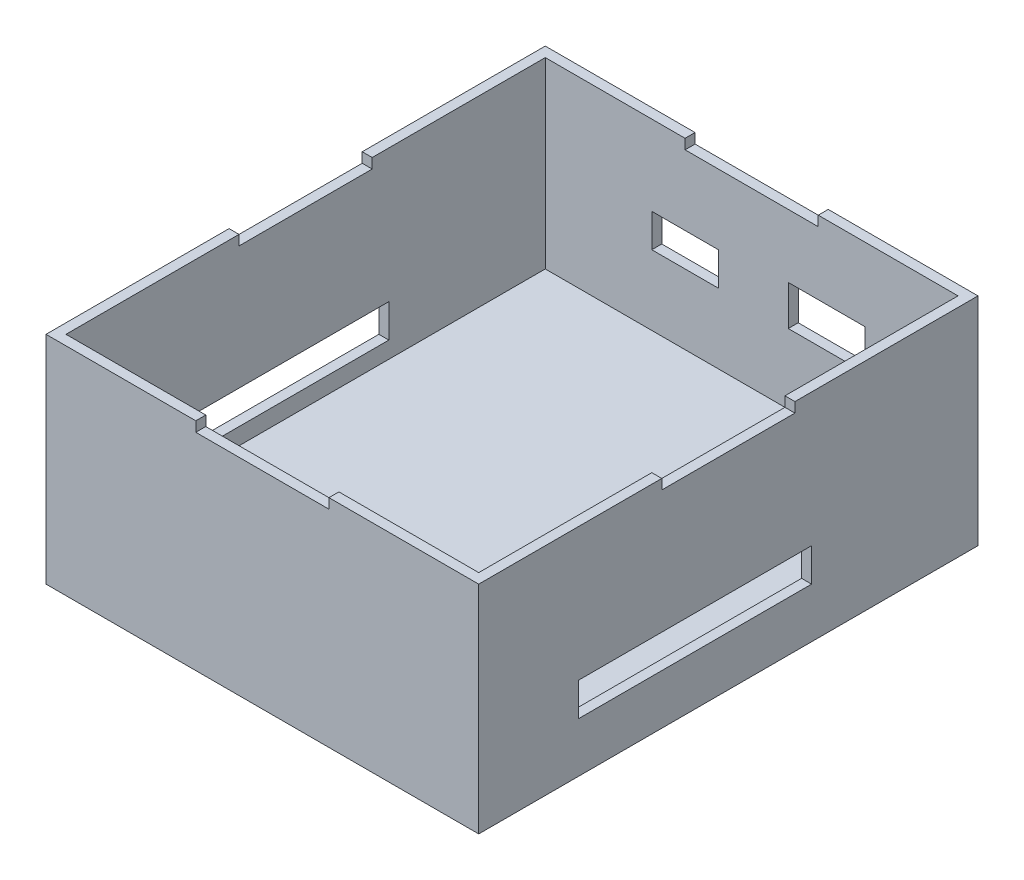
SolidWorks part; units mm, degrees
ref_plane "Plano frontal" through (0, 0, 0) normal (0, 0, 1) x (1, 0, 0)
ref_plane "Plano superior" through (0, 0, 0) normal (0, 1, 0) x (1, 0, 0)
ref_plane "Plano direito" through (0, 0, 0) normal (1, 0, 0) x (0, 0, -1)
sketch "Esboço1" plane through (0, 0, 0) normal (0, 0, 1) x (1, 0, 0)
  line L1 (-52.9398, 41.4834) -> (77.0602, 41.4834)
  line L2 (-52.9398, 41.4834) -> (-52.9398, -23.5166)
  line L3 (-52.9398, -23.5166) -> (77.0602, -23.5166)
  line L4 (77.0602, 41.4834) -> (77.0602, -23.5166)
  dimension "D1" = 130
  dimension "D2" = 65
extrude "Ressalto-extrusão1" add sketch "Esboço1" along normal blind 150
sketch "Esboço2" plane through (-52.9398, 0, 0) normal (-1, 0, 0) x (0, 0, 1)
  line L1 (50, 1.4834) -> (120, 1.4834)
  line L2 (50, 1.4834) -> (50, -8.5166)
  line L3 (50, -8.5166) -> (120, -8.5166)
  line L4 (120, 1.4834) -> (120, -8.5166)
  line L5 (150, -23.5166) -> (0, -23.5166) construction
  line L7 (150, 41.4834) -> (150, -23.5166) construction
  dimension "D1" = 25
  dimension "D2" = 10
  dimension "D3" = 70
  dimension "D4" = 30
extrude "Corte-extrusão1" cut sketch "Esboço2" against normal through all
sketch "Esboço3" plane through (-52.9398, 0, 0) normal (-1, 0, 0) x (0, 0, 1)
  line L0 (150, 41.4834) -> (0, 41.4834) construction
  line L1 (55, 41.4834) -> (95, 41.4834)
  line L2 (55, 41.4834) -> (55, 38.4834)
  line L3 (55, 38.4834) -> (95, 38.4834)
  line L4 (95, 41.4834) -> (95, 38.4834)
  line L5 (150, 41.4834) -> (150, -23.5166) construction
  dimension "D1" = 3
  dimension "D2" = 40
  dimension "D3" = 55
extrude "Corte-extrusão2" cut sketch "Esboço3" against normal through all
sketch "Esboço4" plane through (0, 0, 0) normal (0, 0, -1) x (-1, 0, 0)
  line L0 (-77.0602, 41.4834) -> (52.9398, 41.4834) construction
  line L1 (-32.0602, 41.4834) -> (7.9398, 41.4834)
  line L2 (-32.0602, 41.4834) -> (-32.0602, 38.4834)
  line L3 (-32.0602, 38.4834) -> (7.9398, 38.4834)
  line L4 (7.9398, 41.4834) -> (7.9398, 38.4834)
  line L5 (52.9398, 41.4834) -> (52.9398, -23.5166) construction
  line L6 (-77.0602, -23.5166) -> (-77.0602, 41.4834) construction
  dimension "D1" = 40
  dimension "D2" = 3
  dimension "D3" = 45
  dimension "D4" = 45
extrude "Corte-extrusão3" cut sketch "Esboço4" against normal through all
sketch "Esboço5" plane through (0, 0, 0) normal (0, 0, -1) x (-1, 0, 0)
  line L1 (-2.0602, 17.4834) -> (17.9398, 17.4834)
  line L2 (-2.0602, 17.4834) -> (-2.0602, 7.4834)
  line L3 (-2.0602, 7.4834) -> (17.9398, 7.4834)
  line L4 (17.9398, 17.4834) -> (17.9398, 7.4834)
  line L6 (52.9398, -23.5166) -> (-77.0602, -23.5166) construction
  line L7 (-77.0602, -23.5166) -> (-77.0602, 41.4834) construction
  circle A0 centre (-57.0602, 7.4834) radius 7.5
  dimension "D5" = 15
  dimension "D6" = 31
  dimension "D7" = 20
  dimension "D1" = 20
  dimension "D2" = 10
  dimension "D4" = 41
extrude "Corte-extrusão4" cut sketch "Esboço5" against normal blind 141
sketch "Esboço6" plane through (0, 41.4834, 0) normal (0, 1, 0) x (1, 0, 0)
  line L0 (-52.9398, -55) -> (-52.9398, -95) construction
  line L1 (-49.9398, -3) -> (74.0602, -3)
  line L2 (-49.9398, -3) -> (-49.9398, -147)
  line L3 (-49.9398, -147) -> (74.0602, -147)
  line L4 (74.0602, -3) -> (74.0602, -147)
  line L5 (77.0602, -55) -> (77.0602, -95) construction
  line L6 (32.0602, -150) -> (-7.9398, -150) construction
  dimension "D1" = 3
  dimension "D2" = 3
  dimension "D3" = 3
  dimension "D4" = 3
extrude "Corte-extrusão5" cut sketch "Esboço6" against normal blind 55
sketch "Esboço8" [suppressed] plane through (0, 41.4834, 0) normal (0, 1, 0) x (1, 0, 0)
  line L1 (-49.9398, -3) -> (74.0602, -3)
  line L2 (-49.9398, -3) -> (-49.9398, -147)
  line L3 (-49.9398, -147) -> (74.0602, -147)
  line L4 (74.0602, -3) -> (74.0602, -147)
  line L5 (74.0602, -55) -> (77.0602, -55)
  line L6 (74.0602, -55) -> (74.0602, -95)
  line L7 (74.0602, -95) -> (77.0602, -95)
  line L8 (77.0602, -55) -> (77.0602, -95)
  line L9 (-7.9398, 0) -> (32.0602, 0)
  line L10 (-7.9398, 0) -> (-7.9398, -3)
  line L11 (-7.9398, -3) -> (32.0602, -3)
  line L12 (32.0602, 0) -> (32.0602, -3)
  line L13 (-52.9398, -55) -> (-49.9398, -55)
  line L14 (-52.9398, -55) -> (-52.9398, -95)
  line L15 (-52.9398, -95) -> (-49.9398, -95)
  line L16 (-49.9398, -55) -> (-49.9398, -95)
  line L17 (-7.9398, -150) -> (32.0602, -150)
  line L18 (-7.9398, -150) -> (-7.9398, -147)
  line L19 (-7.9398, -147) -> (32.0602, -147)
  line L20 (32.0602, -150) -> (32.0602, -147)
sketch "Esboço9" plane through (0, 0, 0) normal (0, 0, -1) x (-1, 0, 0)
  line L0 (52.9398, -23.5166) -> (-77.0602, -23.5166) construction
  line L1 (-46.0602, 19.4834) -> (-23.0602, 19.4834)
  line L2 (-46.0602, 19.4834) -> (-46.0602, 7.4834)
  line L3 (-46.0602, 7.4834) -> (-23.0602, 7.4834)
  line L4 (-23.0602, 19.4834) -> (-23.0602, 7.4834)
  circle A0 centre (-57.0602, 7.4834) radius 7.5 construction
  dimension "D1" = 23
  dimension "D2" = 12
  dimension "D3" = 11
  dimension "D4" = 31
extrude "Corte-extrusão6" cut sketch "Esboço9" against normal blind 3
